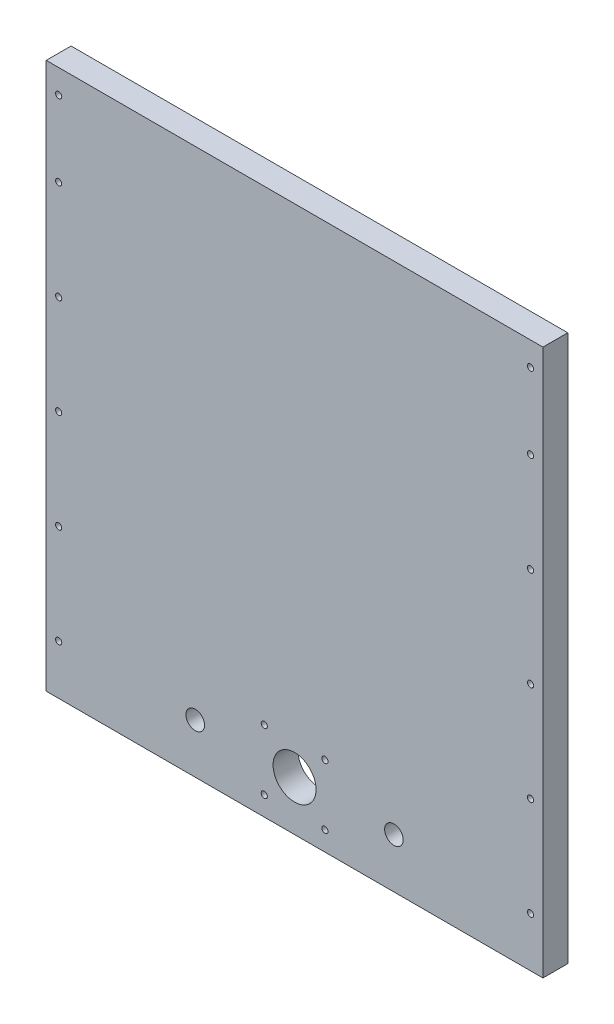
SolidWorks part; units mm, degrees
ref_plane "Front Plane" through (0, 0, 0) normal (0, 0, 1) x (1, 0, 0)
ref_plane "Top Plane" through (0, 0, 0) normal (0, 1, 0) x (1, 0, 0)
ref_plane "Right Plane" through (0, 0, 0) normal (1, 0, 0) x (0, 0, -1)
sketch "Sketch1" plane through (0, 0, 0) normal (0, 0, 1) x (1, 0, 0)
  line L1 (0, 0) -> (254, 0)
  line L2 (0, 0) -> (0, 279.4)
  line L3 (0, 279.4) -> (254, 279.4)
  line L4 (254, 0) -> (254, 279.4)
  circle A0 centre (6.35, 25.4) radius 1.5875
  circle A1 centre (247.65, 25.4) radius 1.5875
  circle A2 centre (6.35, 76.2) radius 1.5875
  circle A3 centre (247.65, 76.2) radius 1.5875
  circle A4 centre (6.35, 127) radius 1.5875
  circle A5 centre (247.65, 127) radius 1.5875
  circle A6 centre (6.35, 177.8) radius 1.5875
  circle A7 centre (247.65, 177.8) radius 1.5875
  circle A8 centre (76.2, 25.4) radius 4.7625
  circle A9 centre (177.8, 25.4) radius 4.7625
  circle A10 centre (127, 25.4) radius 11
  circle A11 centre (142.5, 40.9) radius 1.5875
  circle A12 centre (111.512, 40.9) radius 1.5875
  circle A13 centre (142.5, 9.912) radius 1.5875
  circle A14 centre (111.512, 9.912) radius 1.5875
  circle A15 centre (6.35, 228.6) radius 1.5875
  circle A16 centre (247.65, 228.6) radius 1.5875
  circle A17 centre (6.35, 267.208) radius 1.5875
  circle A18 centre (247.65, 267.208) radius 1.5875
  dimension "D3" = 2
  dimension "D1" = 2
  dimension "D2" = 4
  dimension "D4" = 2
  dimension "D5" = 2
  dimension "D6" = 2
extrude "Boss-Extrude1" add sketch "Sketch1" along normal blind 12.7
